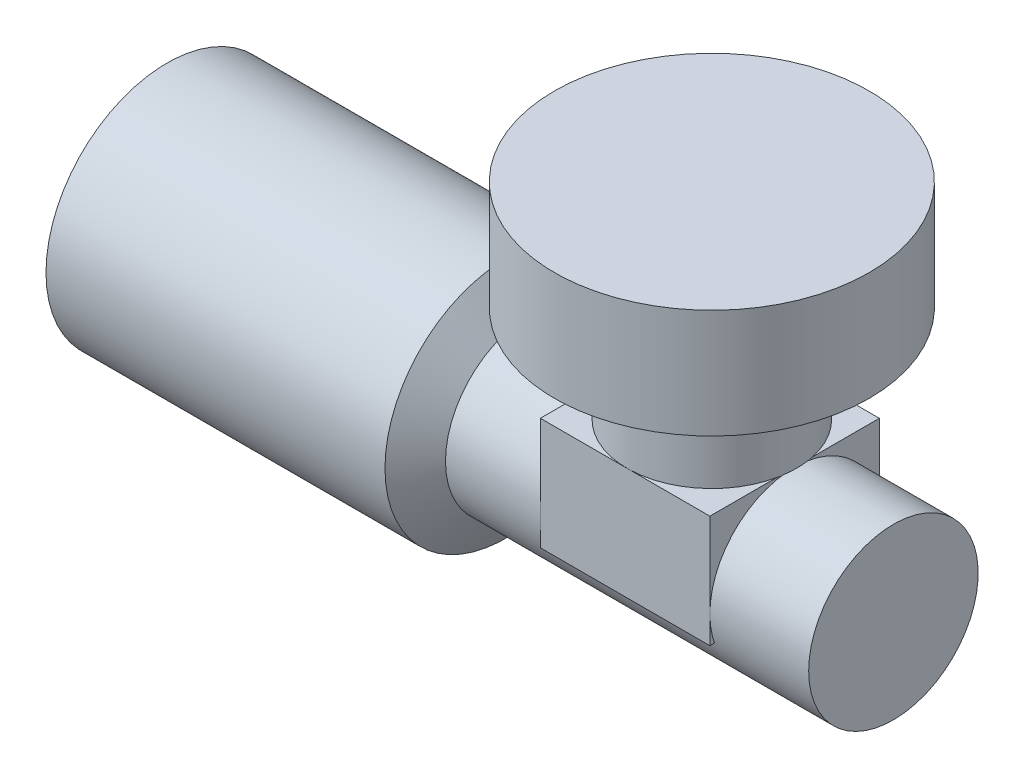
SolidWorks part; units mm, degrees
ref_plane "Front Plane" through (0, 0, 0) normal (0, 0, 1) x (1, 0, 0)
ref_plane "Top Plane" through (0, 0, 0) normal (0, 1, 0) x (1, 0, 0)
ref_plane "Right Plane" through (0, 0, 0) normal (1, 0, 0) x (0, 0, -1)
sketch "Sketch1" plane through (0, 0, 0) normal (0, 1, 0) x (1, 0, 0)
  line L0 (-36.3804, 0) -> (40.1543, 0) construction
  line L1 (0, 31.7743) -> (0, -34.143) construction
  line L2 (-31.3371, 10) -> (-3.3371, 10)
  line L3 (-3.3371, 10) -> (-1.3371, 7)
  line L4 (-1.3371, 7) -> (28.6629, 7)
  line L5 (28.6629, 7) -> (28.6629, 0)
  line L6 (28.6629, 0) -> (-31.3371, 0)
  line L7 (-31.3371, 0) -> (-31.3371, 10)
  dimension "D1" = 7
  dimension "D2" = 10
  dimension "D3" = 28
  dimension "D4" = 60
  dimension "D5" = 30
revolve "Revolve1" add sketch "Sketch1" angle 360 about L0
sketch "Sketch4" plane through (0, 0, 0) normal (0, 0, 1) x (1, 0, 0)
  line L0 (13.6629, 24) -> (13.6629, -25.7431) construction
  line L1 (6.6629, 7) -> (6.6629, 13)
  line L2 (28.6629, 7) -> (-1.3371, 7) construction
  line L3 (6.6629, 13) -> (0.6629, 15)
  line L4 (0.6629, 15) -> (0.6629, 24)
  line L5 (0.6629, 24) -> (13.6629, 24)
  line L6 (13.6629, 24) -> (13.6629, 7)
  line L7 (13.6629, 7) -> (6.6629, 7)
  dimension "D1" = 15
  dimension "D2" = 9
  dimension "D3" = 6
  dimension "D4" = 17
  dimension "D5" = 13
  dimension "D6" = 7
revolve "Revolve2" add sketch "Sketch4" angle 360 about L0
sketch "Sketch5" plane through (0, 0, 0) normal (1, 0, 0) x (0, 0, -1)
  line L1 (-7, 7) -> (7, 7)
  line L2 (-7, 7) -> (-7, -2.2692)
  line L3 (-7, -2.2692) -> (7, -2.2692)
  line L4 (7, 7) -> (7, -2.2692)
extrude "Boss-Extrude2" add sketch "Sketch5" along normal mid plane 14 from offset 13.5 separate body
